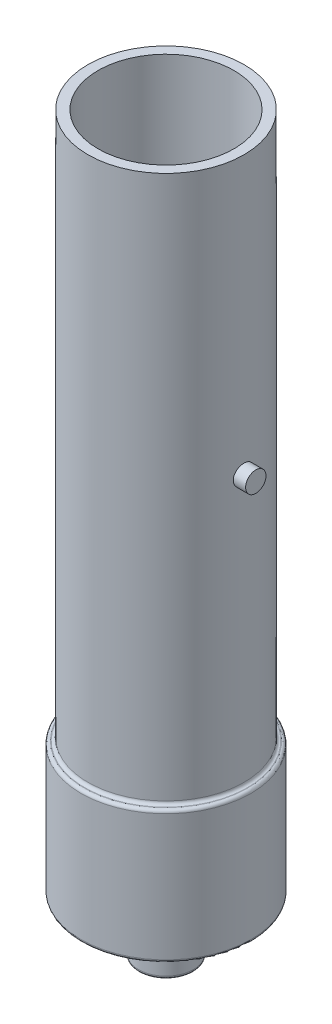
SolidWorks part; units mm, degrees
ref_plane "Front Plane" through (0, 0, 0) normal (0, 0, 1) x (1, 0, 0)
ref_plane "Top Plane" through (0, 0, 0) normal (0, 1, 0) x (1, 0, 0)
ref_plane "Right Plane" through (0, 0, 0) normal (1, 0, 0) x (0, 0, -1)
sketch "Sketch1" plane through (0, 0, 0) normal (0, 1, 0) x (1, 0, 0)
  circle A0 centre (0, 0) radius 10
  circle A1 centre (0, 0) radius 8.7
  dimension "D1" = 20
  dimension "D2" = 1.3
extrude "Boss-Extrude1" add sketch "Sketch1" along normal blind 87
sketch "Sketch2" plane through (0, 0, 0) normal (0, -1, 0) x (1, 0, 0)
  circle A0 centre (0, 0) radius 10.87
  dimension "D1" = 21.74
extrude "Boss-Extrude2" add sketch "Sketch2" against normal blind 17
sketch "Sketch3" plane through (0, 0, 0) normal (0, -1, 0) x (1, 0, 0)
  circle A0 centre (0, 0) radius 3.52
  dimension "D1" = 7.04
extrude "Boss-Extrude3" add sketch "Sketch3" along normal blind 7
sketch "Sketch4" plane through (0, 17, 0) normal (0, 1, 0) x (1, 0, 0)
  circle A1 centre (0, 0) radius 8.7
  circle A2 centre (0, 0) radius 8.7
  dimension "D1" = 0
extrude "Cut-Extrude1" cut sketch "Sketch4" against normal offset from surface (14 mm away) 3 up to face at (0, 0, -3.52)
ref_plane "Plane1" through (10, 0, 0) normal (1, 0, 0) x (0, 0, -1)
sketch "Sketch5" plane through (10, 0, 0) normal (1, 0, 0) x (0, 0, -1)
  line L0 (10, 87) -> (-10, 87) construction
  circle A0 centre (0, 51.5) radius 1.305
  point P2 (24.1283, 63.8772)
  dimension "D1" = 2.61
  dimension "D2" = 35.5
extrude "Boss-Extrude4" add sketch "Sketch5" along normal blind 1.5 and the other way up to surface
fillet "Fillet1" radius 0.4 5 edges at (0, -7, -3.52) (0, 0, -3.52) (0, 17, -10.87) (0, 0, -10.87) (0, 17, -10)
